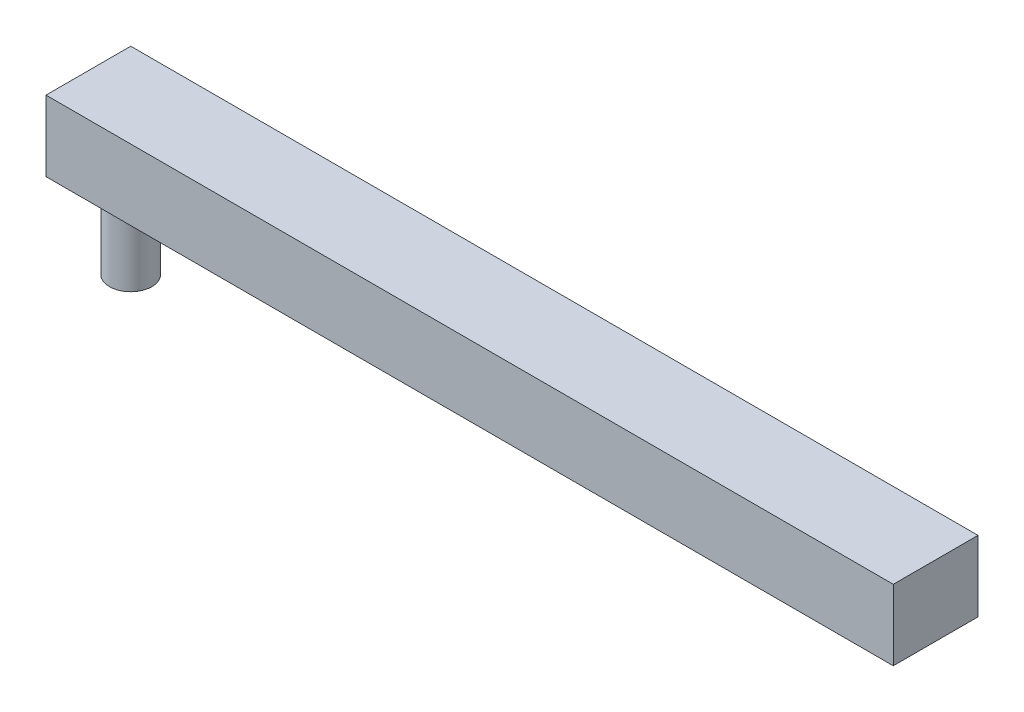
SolidWorks part; units mm, degrees
ref_plane "Front Plane" through (0, 0, 0) normal (0, 0, 1) x (1, 0, 0)
ref_plane "Top Plane" through (0, 0, 0) normal (0, 1, 0) x (1, 0, 0)
ref_plane "Right Plane" through (0, 0, 0) normal (1, 0, 0) x (0, 0, -1)
sketch "Sketch1" plane through (0, -9.9285, 0) normal (0, 1, 0) x (1, 0, 0)
  line L0 (52.6836, -6.9358) -> (-2.8206, -6.9358)
  line L1 (2.6836, -6.9358) -> (52.6836, -6.9358) construction
  line L3 (-2.8206, -6.9358) -> (-7.3164, -6.9358)
  line L4 (-7.3164, -6.9358) -> (-7.3164, -0.9358)
  line L5 (-7.3164, -0.9358) -> (52.6836, -0.9358)
  line L7 (52.6836, -0.9358) -> (52.6836, -6.9358)
  dimension "D1" = 60
  dimension "D2" = 6
extrude "Boss-Extrude1" add sketch "Sketch1" along normal blind 5
sketch "Sketch2" plane through (0, -9.9285, 0) normal (0, -1, 0) x (1, 0, 0)
  line L0 (-4.3164, 0.9358) -> (-4.3164, 6.9358) construction
  line L1 (52.6836, 0.9358) -> (-7.3164, 0.9358) construction
  line L2 (-7.3164, 6.9358) -> (52.6836, 6.9358) construction
  line L3 (-7.3164, 0.9358) -> (-7.3164, 6.9358) construction
  circle A0 centre (-4.3164, 3.9358) radius 1.5
  point P4 (-4.3164, 3.9358)
  dimension "D2" = 3
  dimension "D1" = 3
extrude "Boss-Extrude2" add sketch "Sketch2" along normal blind 6
